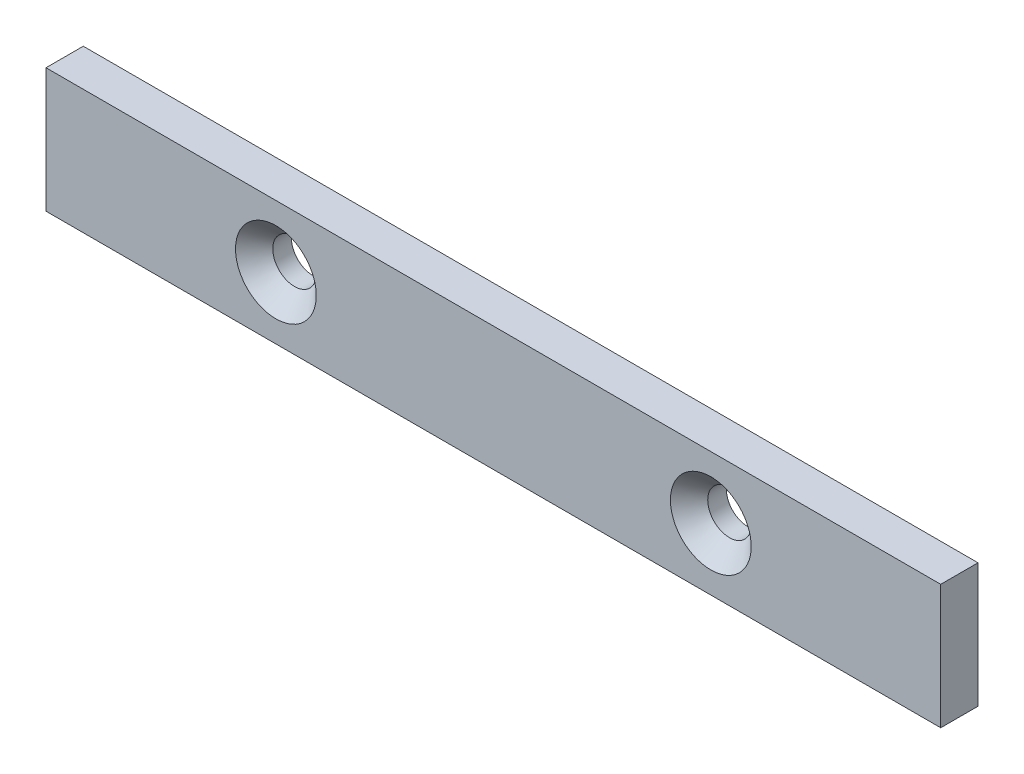
SolidWorks part; units mm, degrees
ref_plane "Front Plane" through (0, 0, 0) normal (0, 0, 1) x (1, 0, 0)
ref_plane "Top Plane" through (0, 0, 0) normal (0, 1, 0) x (1, 0, 0)
ref_plane "Right Plane" through (0, 0, 0) normal (1, 0, 0) x (0, 0, -1)
sketch "Sketch1" plane through (0, 0, 0) normal (0, 0, 1) x (1, 0, 0)
  line L1 (-72, -10) -> (72, -10)
  line L2 (-72, -10) -> (-72, 10)
  line L3 (-72, 10) -> (72, 10)
  line L4 (72, -10) -> (72, 10)
  circle A0 centre (35, 0) radius 3.5
  circle A1 centre (-35, 0) radius 3.5
  point P0 (0, 0)
  point P7 (0, 0)
  point P9 (0, 0)
  dimension "D3" = 7
  dimension "D4" = 7
  dimension "D1" = 20
  dimension "D2" = 144
extrude "Boss-Extrude1" add sketch "Sketch1" along normal mid plane 6
chamfer "Chamfer1" distance 3 angle 45 2 edges at (38.5, 0, 3) (-31.5, 0, 3)
